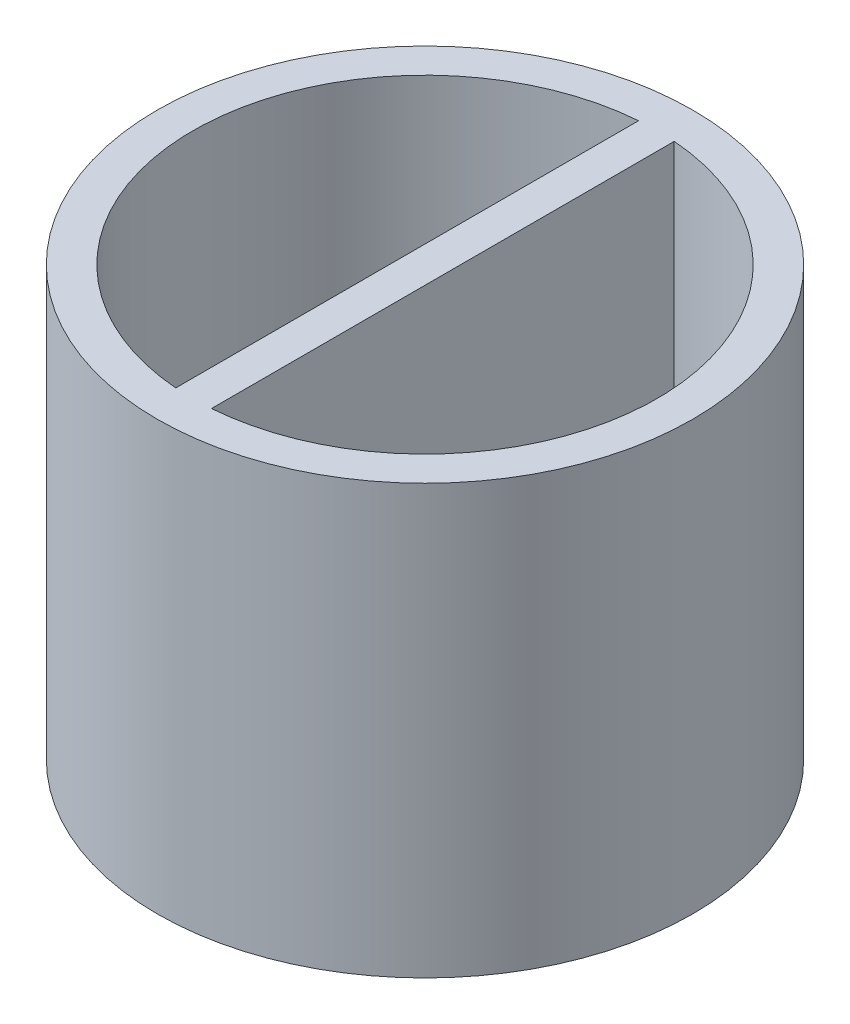
SolidWorks part; units mm, degrees
ref_plane "Front Plane" through (0, 0, 0) normal (0, 0, 1) x (1, 0, 0)
ref_plane "Top Plane" through (0, 0, 0) normal (0, 1, 0) x (1, 0, 0)
ref_plane "Right Plane" through (0, 0, 0) normal (1, 0, 0) x (0, 0, -1)
sketch "Sketch1" plane through (0, 0, 0) normal (0, 1, 0) x (1, 0, 0)
  circle A0 centre (0, 0) radius 37.5
  dimension "D1" = 75
extrude "Boss-Extrude1" add sketch "Sketch1" along normal blind 60
sketch "Sketch2" plane through (0, 60, 0) normal (0, 1, 0) x (1, 0, 0)
  line L2 (-2.5, 32.4037) -> (-2.5, -32.4037)
  line L4 (2.5, 32.4037) -> (2.5, -32.4037)
  line L5 (-2.1619, 32.428) -> (2.1619, -32.428) construction
  line L6 (-2.1619, -32.428) -> (2.1619, 32.428) construction
  circle A0 centre (0, 0) radius 32.5
  dimension "D1" = 65
  dimension "D2" = 64.8074
  dimension "D3" = 64.8074
extrude "Cut-Extrude1" cut sketch "Sketch2" against normal blind 50 contours L2 A0 | L4 A0
sketch "Sketch3" plane through (0, 0, 0) normal (0, -1, 0) x (1, 0, 0)
  circle A0 centre (0, 0) radius 10.35
  dimension "D1" = 20.7
extrude "Cut-Extrude2" cut sketch "Sketch3" against normal blind 5
